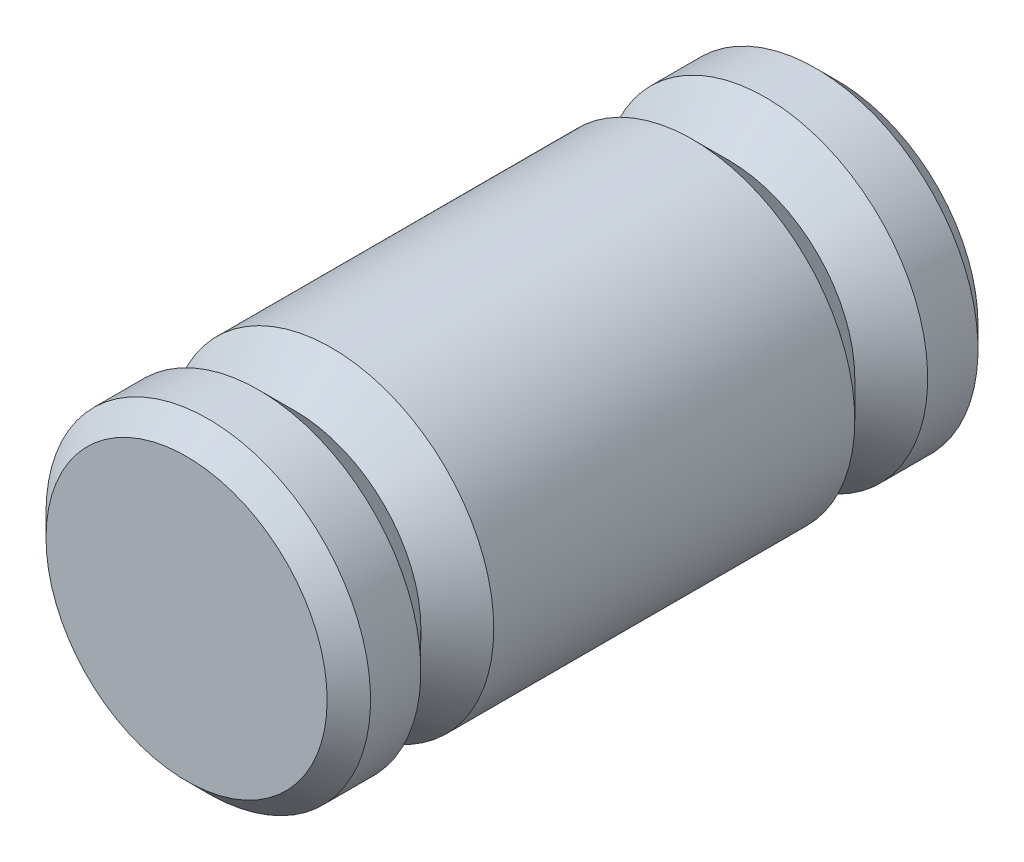
SolidWorks part; units mm, degrees
ref_plane "Front Plane" through (0, 0, 0) normal (0, 0, 1) x (1, 0, 0)
ref_plane "Top Plane" through (0, 0, 0) normal (0, 1, 0) x (1, 0, 0)
ref_plane "Right Plane" through (0, 0, 0) normal (1, 0, 0) x (0, 0, -1)
sketch "Sketch1" plane through (0, 0, 0) normal (0, 0, 1) x (1, 0, 0)
  circle A0 centre (22.4599, 0) radius 4.7498
  dimension "D1" = 9.4996
extrude "Extrude1" add sketch "Sketch1" along normal up to surface (11.43 mm away)
sketch "Sketch2" plane through (0, 0, 0) normal (0, 1, 0) x (-1, 0, 0)
  line L3 (-22.4599, 5.08) -> (-14.3016, 5.08) construction
  line L5 (-22.4599, 11.43) -> (-22.4599, 1.0759) construction
  line L6 (-17.7101, 11.43) -> (-27.2098, 11.43) construction
  line L8 (-12.1293, 11.43) -> (-28.81, 11.43) construction
  line L9 (-18.7769, 5.08) -> (-16.8719, 6.985)
  line L10 (-18.7769, 5.08) -> (-16.8719, 3.175)
  line L11 (-16.8719, 6.985) -> (-16.8719, 3.175)
  dimension "D3" = 6.35
  dimension "D4" = 3.683
  dimension "D5" = 1.905
revolve "Cut-Revolve1" cut sketch "Sketch2" angle 360 about L5
sketch "Sketch3" plane through (0, 0, 0) normal (0, 0, -1) x (-1, 0, 0)
  circle A1 centre (-22.4599, 0) radius 4.7498
  circle A2 centre (-22.4599, 0) radius 4.7498
  dimension "D1" = 0
extrude "Cut-Extrude1" cut sketch "Sketch3" against normal blind 1.905
chamfer "Chamfer1" distance 0.635 1 edges at (17.7101, 0, 1.905)
mirror "Mirror1" about plane through (28.81, -13.97, 11.43) normal (0, 0, -1) of "Cut-Extrude1", "Cut-Revolve1", "Extrude1", "Chamfer1"
